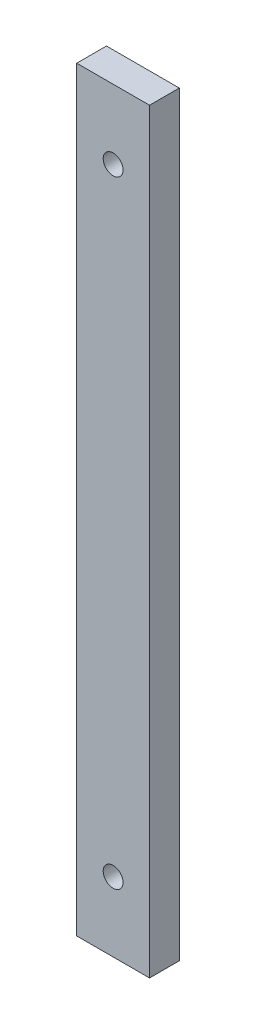
SolidWorks part; units mm, degrees
material "Acrylic (Medium-high impact)"
ref_plane "Front Plane" through (0, 0, 0) normal (0, 0, 1) x (1, 0, 0)
ref_plane "Top Plane" through (0, 0, 0) normal (0, 1, 0) x (1, 0, 0)
ref_plane "Right Plane" through (0, 0, 0) normal (1, 0, 0) x (0, 0, -1)
sketch "Sketch1" plane through (0, 0, 0) normal (0, 0, 1) x (1, 0, 0)
  line L1 (-7.34, 76.2) -> (7.34, 76.2)
  line L2 (-7.34, 76.2) -> (-7.34, -76.2)
  line L3 (-7.34, -76.2) -> (7.34, -76.2)
  line L4 (7.34, 76.2) -> (7.34, -76.2)
  line L5 (-7.34, 76.2) -> (7.34, -76.2) construction
  line L6 (-7.34, -76.2) -> (7.34, 76.2) construction
  point P0 (0, 0)
  dimension "D1" = 14.68
  dimension "D2" = 152.4
extrude "Boss-Extrude1" add sketch "Sketch1" along normal blind 6
sketch "Sketch2" plane through (0, 0, 6) normal (0, 0, 1) x (1, 0, 0)
  line L0 (0, -76.2) -> (0, -62.2)
  line L1 (-7.34, 76.2) -> (7.34, 76.2)
  line L2 (-7.34, 76.2) -> (-7.34, -76.2)
  line L3 (-7.34, -76.2) -> (7.34, -76.2)
  line L4 (7.34, 76.2) -> (7.34, -76.2)
  line L5 (-7.34, 0) -> (7.34, 0)
  circle A0 centre (0, -62.2) radius 2
  circle A1 centre (0, 62.2) radius 2
extrude "Cut-Extrude1" cut sketch "Sketch2" against normal blind 6
